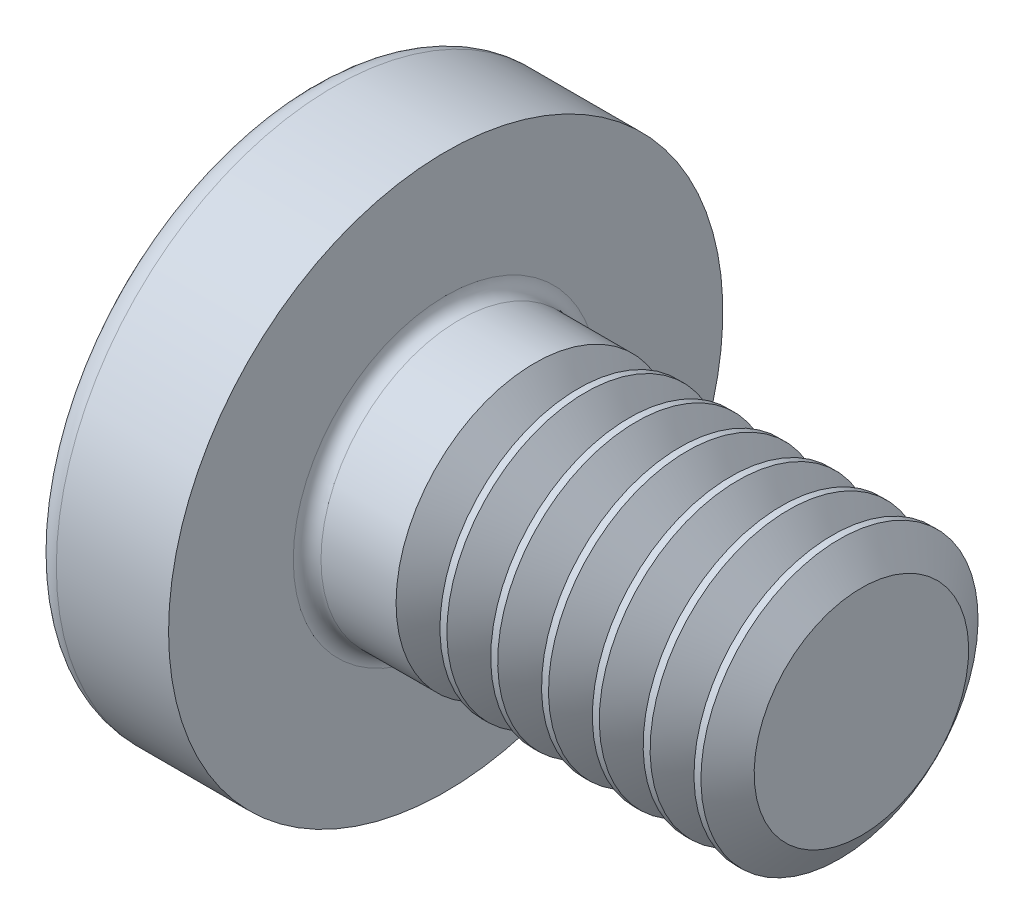
SolidWorks part; units mm, degrees
ref_plane "Plane1" through (0, 0, 0) normal (0, 0, 1) x (1, 0, 0)
ref_plane "Plane2" through (0, 0, 0) normal (0, 1, 0) x (1, 0, 0)
ref_plane "Plane3" through (0, 0, 0) normal (1, 0, 0) x (0, 0, -1)
sketch "BodySke" plane through (0, 0, 0) normal (0, 0, 1) x (1, 0, 0)
  line L0 (1.6, 1) -> (1.6, 2)
  line L1 (1.8, 6.35) -> (1.8, -3.175) construction
  line L2 (-25.4, 0) -> (127, 0) construction
  line L3 (4.6, 0) -> (0, 0)
  line L4 (1.6, 1) -> (4.6, 1)
  line L5 (4.6, 1) -> (4.6, 0)
  line L6 (0.79, 2) -> (1.6, 2)
  line L8 (1.6, 6.35) -> (1.6, -3.175) construction
  arc A0 (0.6464, 1.9285) -> (0, 0) centre (3.2, 0) ccw
  arc A2 (0.6464, 1.9285) -> (0.79, 2) centre (0.79, 1.82) cw
revolve "Base-Revolve" add sketch "BodySke"
cosmetic thread "ThreadCosmetic" [suppressed]
fillet "Fillet1" radius 0.1 1 edges at (1.6, 0, 1)
sketch "Sketch3" plane through (0, 0, 0) normal (1, 0, 0) x (0, 0, -1)
  line L0 (0.24, -1.05) -> (-0.24, -1.05)
  line L1 (0.24, -1.05) -> (0.24, 1.05)
  line L2 (-0.24, 1.05) -> (0.24, 1.05)
  line L3 (-0.24, 1.05) -> (-0.24, -1.05)
ref_plane "Plane4" through (1.42, 0, 0) normal (1, 0, 0) x (0, 0, -1)
sketch "Sketch4" plane through (1.42, 0, 0) normal (1, 0, 0) x (0, 0, -1)
  line L0 (0.24, -0.342) -> (-0.24, -0.342)
  line L1 (0.24, -0.342) -> (0.24, 0.342)
  line L2 (-0.24, 0.342) -> (0.24, 0.342)
  line L3 (-0.24, 0.342) -> (-0.24, -0.342)
loft "Recess" cut profiles "Sketch3", "Sketch4"
pattern_circular "RecPat" count 2 every 90 about axis through (0, 0, 0) along (1, 0, 0) of "Recess"
sketch "RecCorSke" plane through (0, 0, 0) normal (0, 0, 1) x (1, 0, 0)
  line L0 (-3.175, 0) -> (15.875, 0) construction
  line L1 (-25.4, 0) -> (127, 0) construction
  line L2 (0, 0) -> (0, 0.4548)
  line L3 (0, 0.4548) -> (1.42, 0.3555)
  line L4 (1.42, 0.3555) -> (1.5355, 0)
  line L5 (1.5355, 0) -> (0, 0)
revolve "RecessCore" cut sketch "RecCorSke" angle 360 about L0
sketch "ThdSchSke" plane through (0, 0, 0) normal (0, 0, 1) x (1, 0, 0)
  line L0 (2.4, -0.774) -> (2.2418, -1)
  line L1 (2.4, -0.774) -> (2.5582, -1)
  line L2 (2.5582, -1) -> (2.5582, -1.25)
  line L3 (-3.175, 0) -> (5.1513, 0) construction
  line L5 (2.5582, -1.25) -> (2.2418, -1.25)
  line L6 (2.2418, -1.25) -> (2.2418, -1)
revolve "ThreadSchematic" cut sketch "ThdSchSke" angle 360 about L3
pattern_linear "ThdSchPat" count 7 spacing 0.3667 along (1, 0, 0) of "ThreadSchematic"
equation "\"D1@Sketch3\" = \"Cross_dia@Sketch3\" / 2"
equation "\"D2@Sketch3\" = \"Cross_width@Sketch3\" / 2"
equation "\"Depth@RecCorSke\" = \"Cross_depth@Plane4\""
equation "\"D1@Sketch4\" = \"Cross_width@Sketch3\""
equation "\"D2@Sketch4\" = \"Cross_dia@Sketch3\" - 2.0 * \"Cross_depth@Plane4\" * tan(26.5  * 0.017453292)"
equation "\"D3@Sketch4\" = \"D1@Sketch4\" / 2"
equation "\"D4@Sketch4\" = \"D2@Sketch4\" / 2"
equation "\"Thread_length@ThreadCosmetic\" = ((sgn( (\"Length@BodySke\" - \"Advance@BodySke\" * 2.0 ) - \"Thread_nom@BodySke\" )-1)*( (\"Length@BodySke\" - \"Advance@BodySke\" * 2.0 ) - \"Thread_nom@BodySke\" ))/-2+ \"Thread_nom@BodySke\""
equation "\"Thread_minor@ThdSchSke\" = \"Thread_minor@ThreadCosmetic\""
equation "\"Diameter@ThdSchSke\" = \"Diameter@BodySke\""
equation "\"Overcut@ThdSchSke\" = \"Diameter@BodySke\" * 1.25"
equation "\"Start@ThdSchSke\" = \"Head_ht@BodySke\" + \"Length@BodySke\" - \"Thread_length@ThreadCosmetic\"  '---Non-countersunk---"
equation "\"Num_threads@ThdSchPat\" = int( \"Thread_length@ThreadCosmetic\" / \"Advance@BodySke\" + 0.999 )  + 1"
equation "\"Advance@ThdSchPat\" = \"Thread_length@ThreadCosmetic\" /  (\"Num_threads@ThdSchPat\" - 1) 'relax it"
